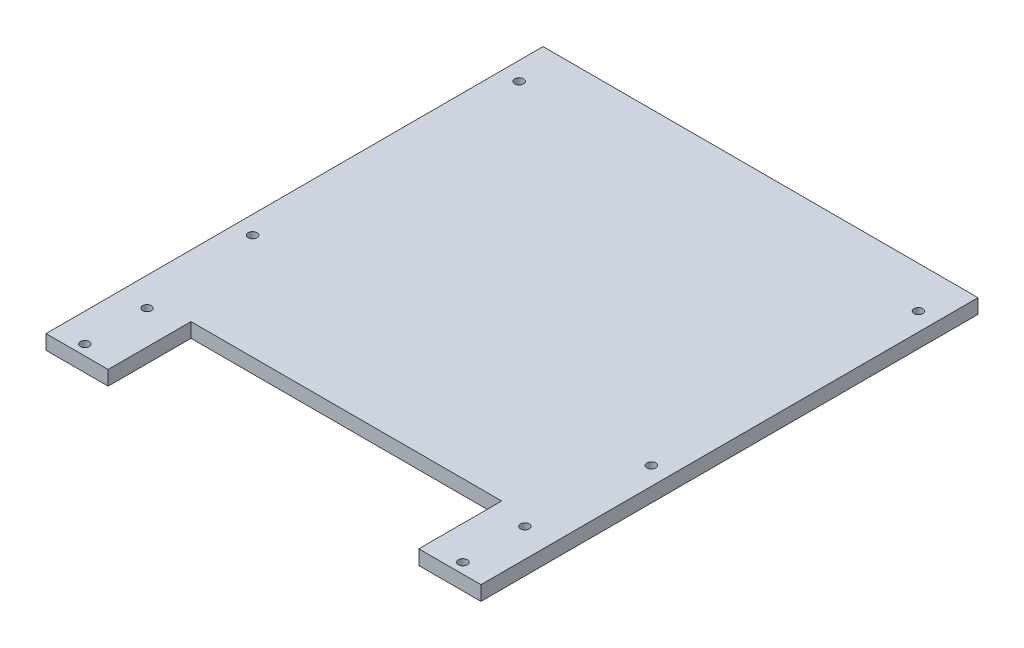
SolidWorks part; units mm, degrees
ref_plane "Alzado" through (0, 0, 0) normal (0, 0, 1) x (1, 0, 0)
ref_plane "Planta" through (0, 0, 0) normal (0, 1, 0) x (1, 0, 0)
ref_plane "Vista lateral" through (0, 0, 0) normal (1, 0, 0) x (0, 0, -1)
sketch "Croquis1" plane through (0, 0, 0) normal (0, 1, 0) x (1, 0, 0)
  line L0 (150, -240) -> (210, -240)
  line L1 (-210, -240) -> (-150, -240)
  line L2 (-210, -240) -> (-210, 240)
  line L3 (-210, 240) -> (210, 240)
  line L4 (210, -240) -> (210, 240)
  line L5 (-210, -240) -> (210, 240) construction
  line L6 (-210, 240) -> (210, -240) construction
  line L8 (-150, -240) -> (-150, -160)
  line L9 (-150, -160) -> (150, -160)
  line L10 (150, -240) -> (150, -160)
  point P0 (0, 0)
  dimension "D1" = 480
  dimension "D2" = 420
  dimension "D3" = 60
  dimension "D4" = 300
  dimension "D5" = 80
extrude "Saliente-Extruir1" add sketch "Croquis1" along normal blind 14
sketch "Croquis2" plane through (0, 14, 0) normal (0, 1, 0) x (1, 0, 0)
  line L0 (210, -240) -> (210, 240) construction
  line L1 (-210, 240) -> (-210, -240) construction
  line L3 (150, -240) -> (210, -240) construction
  line L4 (-210, -240) -> (-150, -240) construction
  line L5 (210, 240) -> (-210, 240) construction
  circle A0 centre (-182.5, -230) radius 4.25
  circle A1 centre (-182.5, -170) radius 4.25
  circle A2 centre (-192.5, -58) radius 4.25
  circle A3 centre (-192.5, 199.3885) radius 4.25
  circle A4 centre (192.4995, 200) radius 4.25
  circle A5 centre (192.5, -58) radius 4.25
  circle A6 centre (182.5, -170) radius 4.25
  circle A7 centre (182.5, -230) radius 4.25
  dimension "D3" = 8.5
  dimension "D4" = 8.5
  dimension "D5" = 8.5
  dimension "D8" = 8.5
  dimension "D13" = 8.5
  dimension "D14" = 8.5
  dimension "D17" = 8.5
  dimension "D18" = 8.5
  dimension "D1" = 365
  dimension "D2" = 27.5
  dimension "D6" = 365
  dimension "D7" = 27.5
  dimension "D9" = 60
  dimension "D10" = 60
  dimension "D11" = 10
  dimension "D12" = 10
  dimension "D15" = 385
  dimension "D16" = 17.5
  dimension "D19" = 385
  dimension "D20" = 17.5
  dimension "D21" = 40
  dimension "D22" = 258
extrude "Cortar-Extruir1" cut sketch "Croquis2" against normal through all
